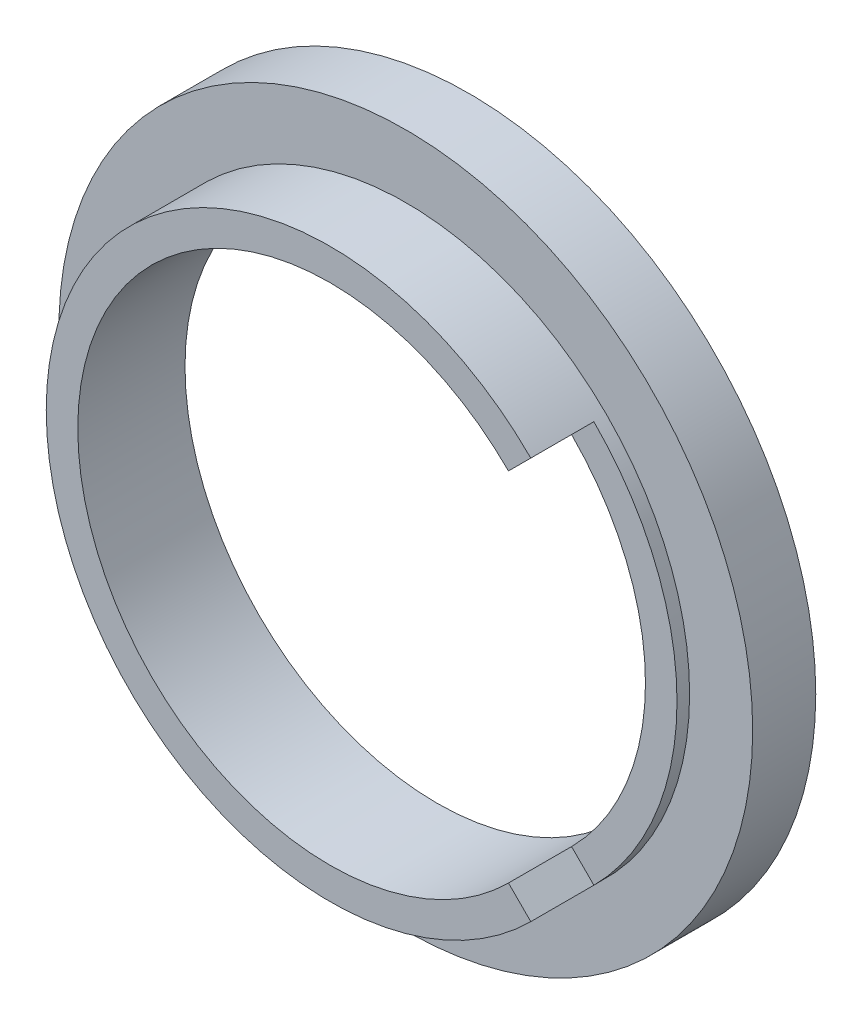
SolidWorks part; units mm, degrees
ref_plane "前视基准面" through (0, 0, 0) normal (0, 0, 1) x (1, 0, 0)
ref_plane "上视基准面" through (0, 0, 0) normal (0, 1, 0) x (1, 0, 0)
ref_plane "右视基准面" through (0, 0, 0) normal (1, 0, 0) x (0, 0, -1)
sketch "草图1" plane through (0, 0, 0) normal (0, 0, 1) x (1, 0, 0)
  circle A0 centre (0, 0) radius 11
extrude "凸台-拉伸1" add sketch "草图1" along normal blind 2 contours A0
sketch "草图2" plane through (0, 0, 2) normal (0, 0, 1) x (1, 0, 0)
  circle A0 centre (0, 0) radius 9
extrude "凸台-拉伸2" add sketch "草图2" along normal blind 2.4
sketch "草图3" plane through (0, 0, 0) normal (0, 0, -1) x (-1, 0, 0)
  circle A0 centre (0, 0) radius 10
extrude "切除-拉伸1" cut sketch "草图3" against normal blind 1
sketch "草图4" plane through (0, 0, 1) normal (0, 0, -1) x (-1, 0, 0)
  circle A0 centre (0, 0) radius 8
extrude "切除-拉伸2" cut sketch "草图4" against normal blind 10
sketch "草图5" plane through (0, 0, 4.4) normal (0, 0, 1) x (1, 0, 0)
  line L0 (0, 0) -> (6.364, 6.364)
  line L1 (0, 0) -> (6.364, -6.364)
  circle A0 centre (0, 0) radius 9 construction
  arc A1 (6.364, -6.364) -> (6.364, 6.364) centre (0, 0) ccw
  circle M2 centre (0, 0) radius 8
  circle M3 centre (0, 0) radius 9
extrude "切除-拉伸3" cut sketch "草图5" against normal blind 2 contours L0 L1 M2 | L1 L0 M2 M3
